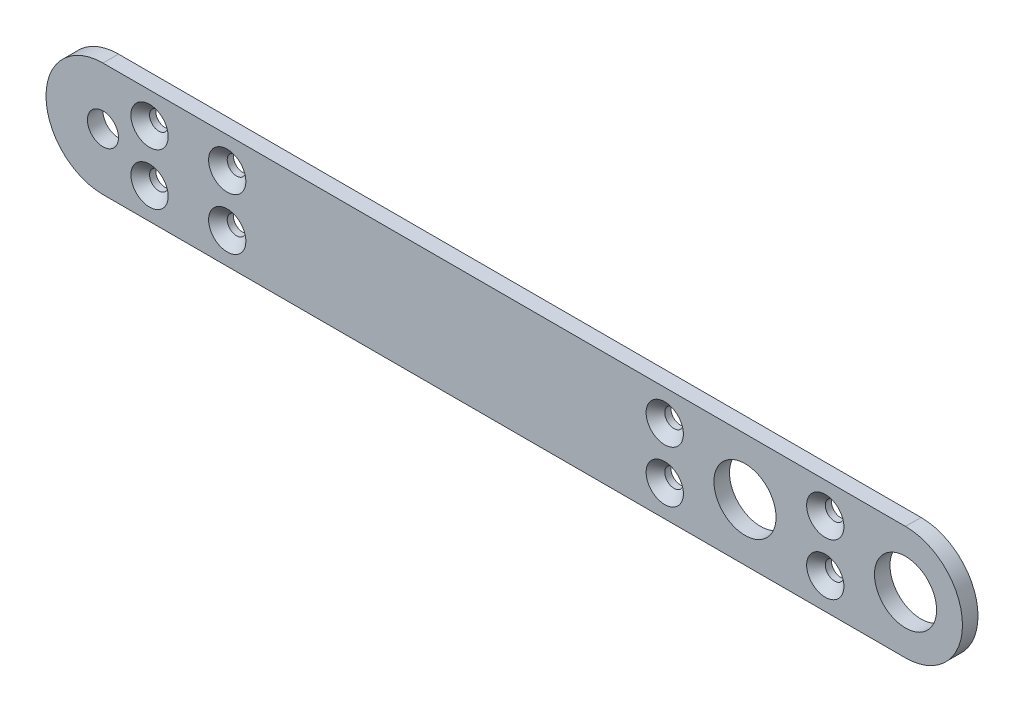
SolidWorks part; units mm, degrees
material "Hexcel AS4C (3000 Filaments)"
ref_plane "Front Plane" through (0, 0, 0) normal (0, 0, 1) x (1, 0, 0)
ref_plane "Top Plane" through (0, 0, 0) normal (0, 1, 0) x (1, 0, 0)
ref_plane "Right Plane" through (0, 0, 0) normal (1, 0, 0) x (0, 0, -1)
sketch "Sketch1" plane through (0, 0, 0) normal (0, 0, 1) x (1, 0, 0)
  line L0 (15.5, 5.5) -> (-62, 5.5)
  line L1 (-62, -5.5) -> (15.5, -5.5)
  line L2 (0, 0) -> (31.9738, 0) construction
  arc A0 (-62, 5.5) -> (-62, -5.5) centre (-62, 0) ccw
  arc A1 (15.5, -5.5) -> (15.5, 5.5) centre (15.5, 0) ccw
  circle A2 centre (-62, 0) radius 1.5
  circle A3 centre (0, 0) radius 3
  circle A4 centre (15.5, 0) radius 3
  dimension "D1" = 6
  dimension "D2" = 15.5
  dimension "D3" = 3
  dimension "D4" = 62
  dimension "D5" = 5.5
extrude "Boss-Extrude1" add sketch "Sketch1" along normal blind 1.5
hole_wizard "CSK for M1.6 Countersunk Flat Head Screw1" positions "Sketch3" profile "Sketch2" countersink size "M1.6" standard "DIN" end condition through all
sketch "Sketch3" plane through (0, 0, 1.5) normal (0, 0, 1) x (1, 0, 0)
  line L0 (0, 0) -> (-68.8863, 0) construction
  line L2 (7.75, -12.0598) -> (7.75, 13.3437) construction
  line L4 (0, 0) -> (0, 9.9697) construction
  circle A0 centre (-62, 0) radius 1.5 construction
  circle A1 centre (0, 0) radius 3 construction
  circle A2 centre (15.5, 0) radius 3 construction
  point P1 (7.75, 2.5)
  point P5 (-7.75, 2.5)
  point P7 (-57.5, 2.5)
  point P11 (-50, 2.5)
  dimension "D1" = 4.5
  dimension "D2" = 12
  dimension "D3" = 5
sketch "Sketch2" plane through (7.75, 2.5, 1.5) normal (1, 0, 0) x (0, -1, 0)
  line L0 (0, 0) -> (0, 1.5)
  line L1 (0, 1.5) -> (0.9, 1.5)
  line L2 (0.9, 1.5) -> (0.9, 0.9)
  line L3 (0.9, 0.9) -> (1.8, 0)
  line L5 (1.8, 0) -> (0, 0)
  line L6 (-0.9, 0.9) -> (-1.8, 0) construction
  line L11 (0, -6.35) -> (0, 107.95) construction
  dimension "Thru Hole Dia." = 1.8
  dimension "Thru Hole Depth" = 1.5
  dimension "Near C'Sink Dia." = 3.6
  dimension "Near C'Sink Angle" = 90
mirror "Mirror1" about plane through (0, 0, 0) normal (0, 1, 0) of "CSK for M1.6 Countersunk Flat Head Screw1"
